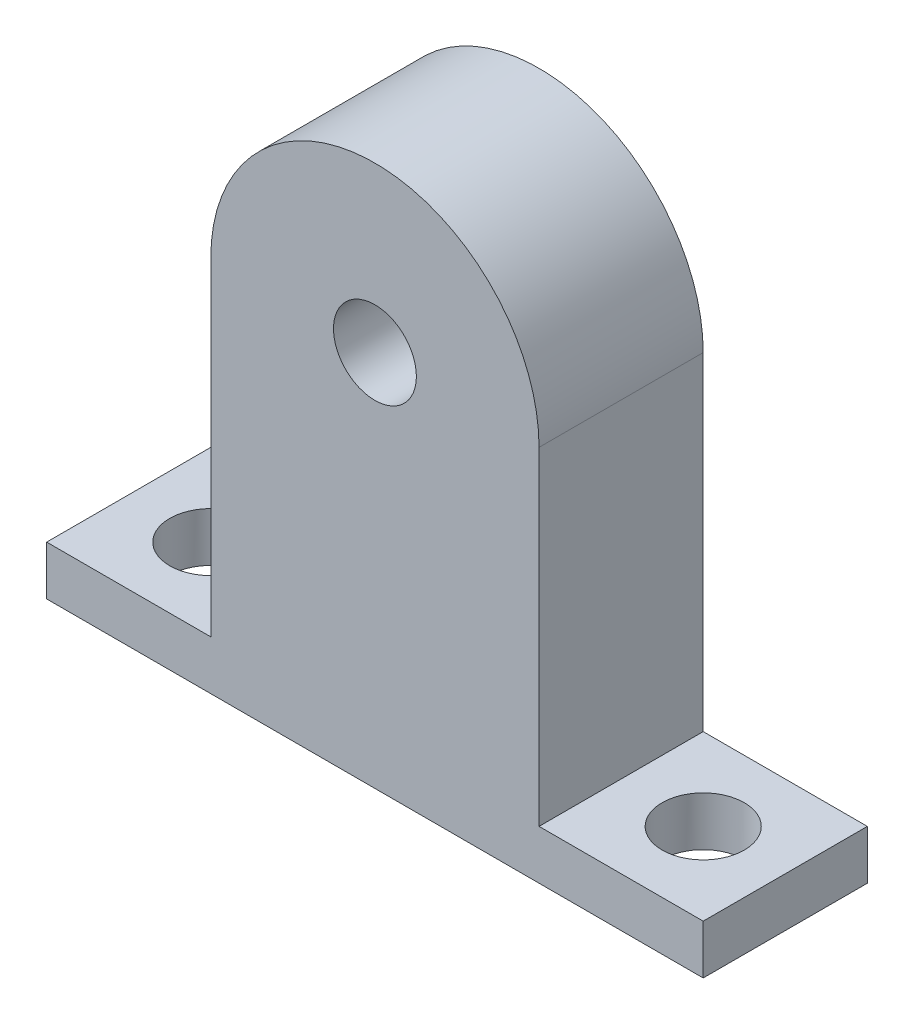
SolidWorks part; units mm, degrees
ref_plane "Front Plane" through (0, 0, 0) normal (0, 0, 1) x (1, 0, 0)
ref_plane "Top Plane" through (0, 0, 0) normal (0, 1, 0) x (1, 0, 0)
ref_plane "Right Plane" through (0, 0, 0) normal (1, 0, 0) x (0, 0, -1)
sketch "Sketch2" plane through (0, 0, 0) normal (0, 1, 0) x (1, 0, 0)
  line L1 (-50.8, -12.7) -> (50.8, -12.7)
  line L2 (-50.8, -12.7) -> (-50.8, 12.7)
  line L3 (-50.8, 12.7) -> (50.8, 12.7)
  line L4 (50.8, -12.7) -> (50.8, 12.7)
  line L5 (-50.8, -12.7) -> (50.8, 12.7) construction
  line L6 (-50.8, 12.7) -> (50.8, -12.7) construction
  point P0 (0, 0)
  dimension "D1" = 25.4
  dimension "D2" = 101.6
extrude "Boss-Extrude1" add sketch "Sketch2" along normal blind 7.62
sketch "Sketch3" plane through (0, 0, 0) normal (0, 0, 1) x (1, 0, 0)
  line L0 (-50.8, 7.62) -> (50.8, 7.62) construction
  line L1 (-25.4, 7.62) -> (25.4, 7.62)
  line L2 (-25.4, 7.62) -> (-25.4, 58.42)
  line L3 (-25.4, 58.42) -> (25.4, 58.42)
  line L4 (25.4, 7.62) -> (25.4, 58.42)
  circle A0 centre (0, 58.42) radius 25.4
  point P6 (0, 7.62)
  point P7 (0, 7.62)
  dimension "D1" = 50.8
  dimension "D2" = 50.8
extrude "Boss-Extrude2" add sketch "Sketch3" along normal mid plane 25.4 contours L3 A0 | L3 A0 | A0 L2 L1 L4
sketch "Sketch4" plane through (0, 7.62, 0) normal (0, 1, 0) x (1, 0, 0)
  circle A0 centre (38.1, 0) radius 6.3563
  dimension "D1" = 12.7127
extrude "Cut-Extrude1" cut sketch "Sketch4" against normal up to next (7.62 mm away)
mirror "Mirror1" about plane through (0, 0, 0) normal (1, 0, 0) of "Cut-Extrude1"
sketch "Sketch5" plane through (0, 0, 12.7) normal (0, 0, 1) x (1, 0, 0)
  circle A0 centre (0, 58.42) radius 6.4135
  dimension "D1" = 12.827
extrude "Cut-Extrude2" cut sketch "Sketch5" against normal up to next
